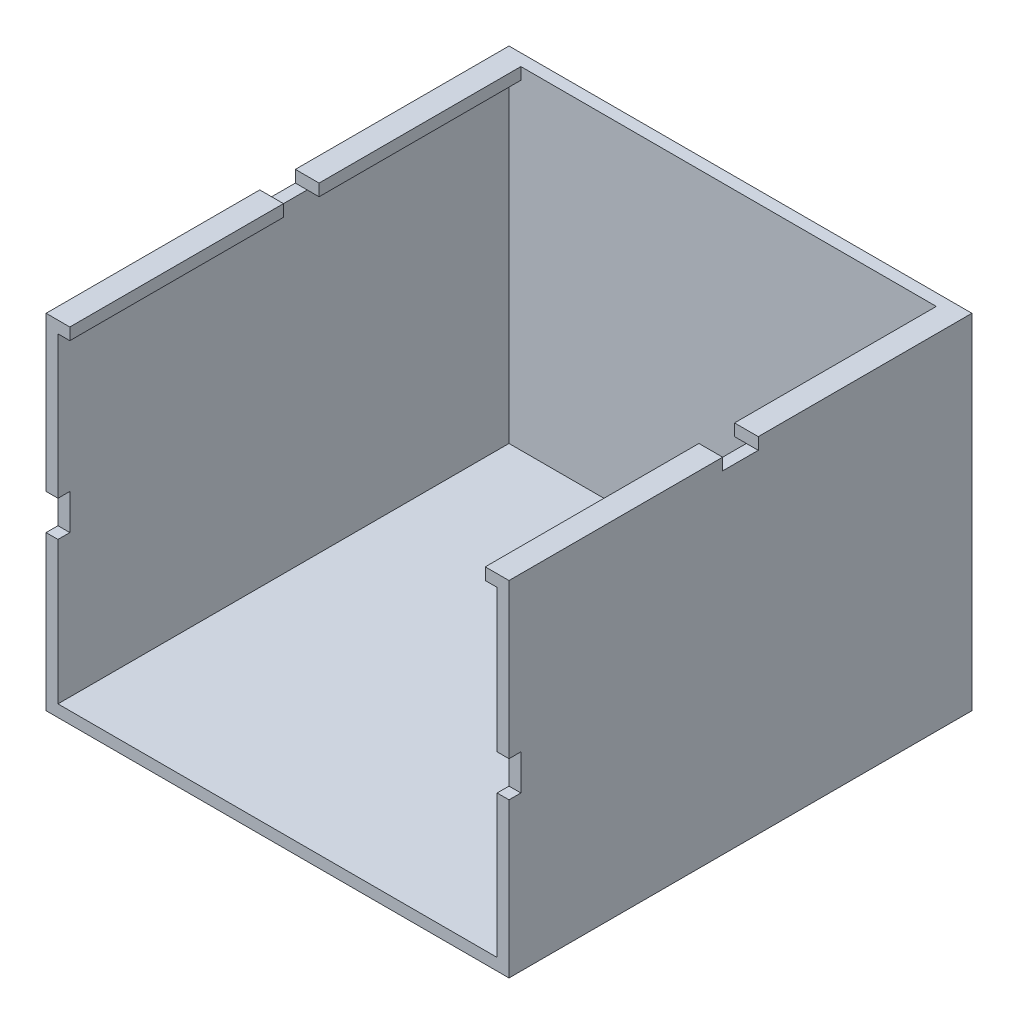
SolidWorks part; units mm, degrees
ref_plane "Front Plane" through (0, 0, 0) normal (0, 0, 1) x (1, 0, 0)
ref_plane "Top Plane" through (0, 0, 0) normal (0, 1, 0) x (1, 0, 0)
ref_plane "Right Plane" through (0, 0, 0) normal (1, 0, 0) x (0, 0, -1)
sketch "Sketch1" plane through (0, 0, 0) normal (0, 1, 0) x (1, 0, 0)
  line L1 (15.4273, -19.6976) -> (-23.5727, -19.6976)
  line L2 (15.4273, -19.6976) -> (15.4273, 19.3024)
  line L3 (15.4273, 19.3024) -> (-23.5727, 19.3024)
  line L4 (-23.5727, -19.6976) -> (-23.5727, 19.3024)
  dimension "D1" = 39
  dimension "D2" = 39
extrude "Boss-Extrude1" add sketch "Sketch1" along normal blind 29
sketch "Sketch3" plane through (0, 0, 19.6976) normal (0, 0, 1) x (1, 0, 0)
  line L0 (-23.5727, 29) -> (-23.5727, 0) construction
  line L1 (-22.5727, 28) -> (14.4273, 28)
  line L2 (-22.5727, 28) -> (-22.5727, 1)
  line L3 (-22.5727, 1) -> (14.4273, 1)
  line L4 (14.4273, 28) -> (14.4273, 1)
  line L5 (-23.5727, 29) -> (15.4273, 29) construction
  dimension "D1" = 27
  dimension "D2" = 37
  dimension "D3" = 1
  dimension "D4" = 1
extrude "Cut-Extrude1" cut sketch "Sketch3" against normal blind 38
sketch "Sketch4" plane through (0, 29, 0) normal (0, 1, 0) x (1, 0, 0)
  line L0 (-23.5727, 19.3024) -> (-23.5727, -19.6976) construction
  line L1 (-21.5727, 18.3024) -> (13.4273, 18.3024)
  line L2 (-21.5727, 18.3024) -> (-21.5727, -20.2856)
  line L3 (-21.5727, -20.2856) -> (13.4273, -20.2856)
  line L4 (13.4273, 18.3024) -> (13.4273, -20.2856)
  line L5 (15.4273, 19.3024) -> (-23.5727, 19.3024) construction
  line L8 (15.4273, -19.6976) -> (15.4273, 19.3024) construction
  dimension "D1" = 2
  dimension "D2" = 1
  dimension "D4" = 2
extrude "Cut-Extrude2" cut sketch "Sketch4" against normal blind 10
sketch "Sketch5" plane through (0, 1, 0) normal (0, 1, 0) x (1, 0, 0)
  line L1 (-24.2886, 1.3024) -> (15.7114, 1.3024)
  line L2 (-24.2886, 1.3024) -> (-24.2886, -1.6976)
  line L3 (-24.2886, -1.6976) -> (15.7114, -1.6976)
  line L4 (15.7114, 1.3024) -> (15.7114, -1.6976)
  line L5 (-23.5727, -19.6976) -> (-21.5727, -19.6976) construction
  line M6 (14.4273, -19.6976) -> (14.4273, 18.3024)
  line M8 (-22.5727, 18.3024) -> (-22.5727, -19.6976)
  dimension "D1" = 3
  dimension "D2" = 40
  dimension "D3" = 18
extrude "Cut-Extrude3" cut sketch "Sketch5" along normal blind 4 from offset 27 contours L3 L1 M8 M6
sketch "Sketch6" plane through (0, 0, -18.3024) normal (0, 0, 1) x (1, 0, 0)
  line L0 (-22.5727, 1) -> (14.4273, 1) construction
  line L1 (-25.3047, 16) -> (16.4727, 16)
  line L2 (-25.3047, 16) -> (-25.3047, 13)
  line L3 (-25.3047, 13) -> (16.4727, 13)
  line L4 (16.4727, 16) -> (16.4727, 13)
  dimension "D1" = 3
  dimension "D2" = 12
extrude "Cut-Extrude5" cut sketch "Sketch6" against normal blind 1 from offset 38
